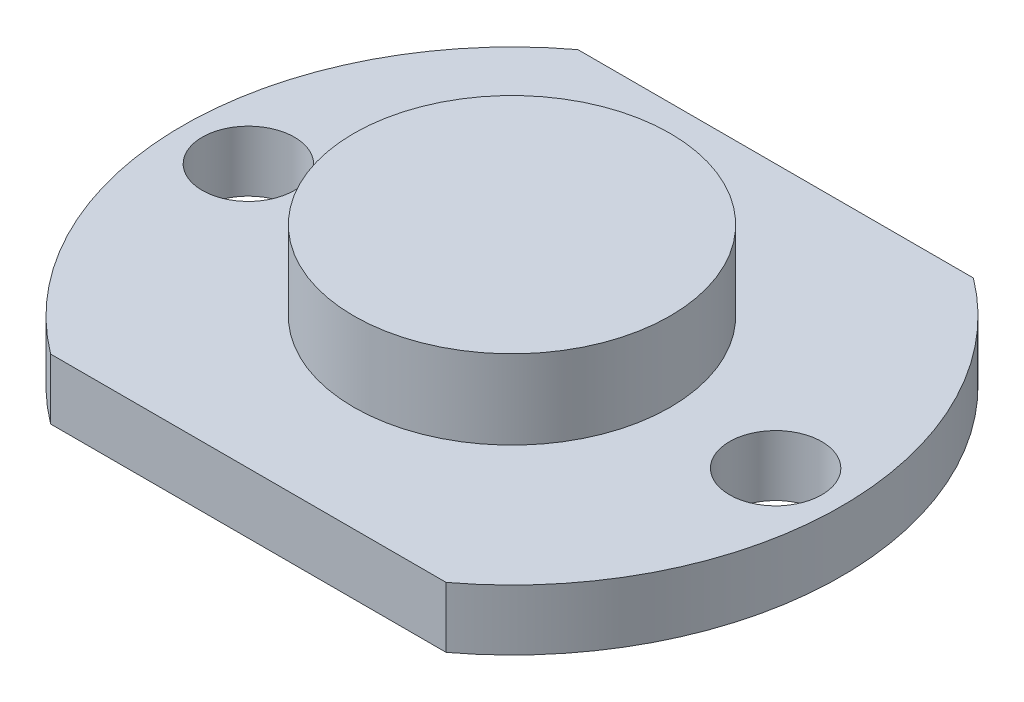
SolidWorks part; units mm, degrees
ref_plane "Front" through (0, 0, 0) normal (0, 0, 1) x (1, 0, 0)
ref_plane "Top" through (0, 0, 0) normal (0, 1, 0) x (1, 0, 0)
ref_plane "Right" through (0, 0, 0) normal (1, 0, 0) x (0, 0, -1)
sketch "Sketch1" plane through (0, 0, 0) normal (0, 1, 0) x (1, 0, 0)
  line L1 (7.5, -10) -> (-7.5, -10)
  line L3 (7.5, 10) -> (-7.5, 10)
  arc A0 (-7.5, 10) -> (-7.5, -10) centre (0, 0) ccw
  circle A1 centre (10, 0) radius 1.75
  circle A2 centre (-10, 0) radius 1.75
  arc A3 (7.5, -10) -> (7.5, 10) centre (0, 0) ccw
  circle A4 centre (0, 0) radius 10 construction
  dimension "D1" = 3.5
  dimension "D4" = 3.5
  dimension "D9" = 12.5
  dimension "D2" = 10
  dimension "D3" = 10
  dimension "D5" = 10
  dimension "D6" = 10
  dimension "D7" = 10
  dimension "D8" = 10
extrude "Boss-Extrude1" add sketch "Sketch1" along normal blind 2.3
sketch "Sketch3" plane through (0, 2.3, 0) normal (0, 1, 0) x (1, 0, 0)
  circle A0 centre (0, 0) radius 6
  dimension "D1" = 12
extrude "Boss-Extrude2" add sketch "Sketch3" along normal blind 3
